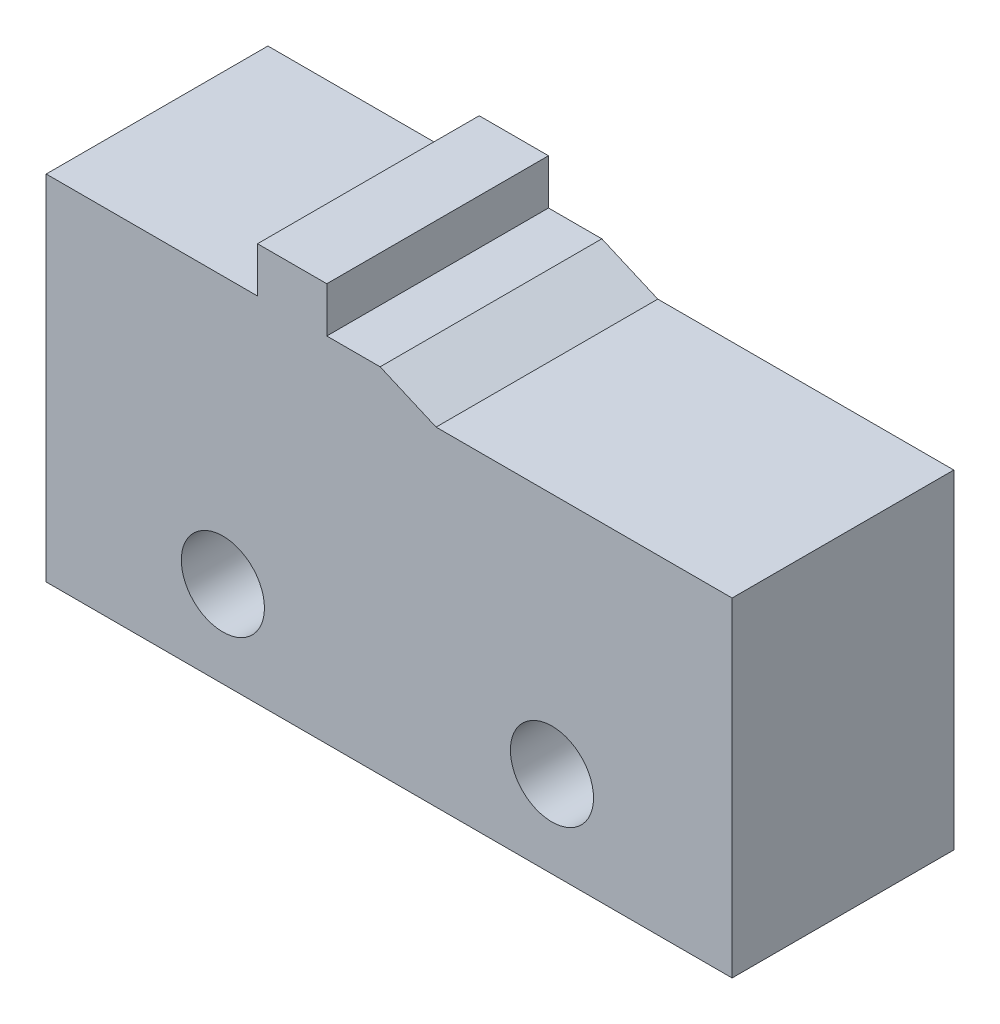
SolidWorks part; units mm, degrees
ref_plane "Front Plane" through (0, 0, 0) normal (0, 0, 1) x (1, 0, 0)
ref_plane "Top Plane" through (0, 0, 0) normal (0, 1, 0) x (1, 0, 0)
ref_plane "Right Plane" through (0, 0, 0) normal (1, 0, 0) x (0, 0, -1)
sketch "Sketch1" plane through (0, 0, 0) normal (0, 0, 1) x (1, 0, 0)
  line L0 (5.1, 2.5) -> (14.6, 2.5) construction
  line L1 (0, 0) -> (19.8, 0)
  line L2 (0, 0) -> (0, 10.2)
  line L3 (0, 10.2) -> (6.1, 10.2)
  line L4 (19.8, 0) -> (19.8, 9.5)
  line L5 (19.8, 9.5) -> (11.2548, 9.5)
  line L6 (11.2548, 9.5) -> (9.64, 10.2)
  line L7 (6.1, 10.2) -> (6.1, 11.5067)
  line L8 (6.1, 11.5067) -> (8.1, 11.5067)
  line L9 (8.1, 11.5067) -> (8.1, 10.2)
  line L10 (8.1, 10.2) -> (9.64, 10.2)
  line L11 (7.1, 11.5067) -> (7.1, 7.3639) construction
  circle A0 centre (5.1, 2.5) radius 1.2
  circle A1 centre (14.6, 2.5) radius 1.2
  dimension "D7" = 5.1
  dimension "D8" = 2.4
  dimension "D1" = 19.8
  dimension "D2" = 10.2
  dimension "D3" = 9.5
  dimension "D4" = 2
  dimension "D5" = 9.5
  dimension "D6" = 2.5
  dimension "D9" = 7.5
extrude "Boss-Extrude1" add sketch "Sketch1" along normal blind 6.4
